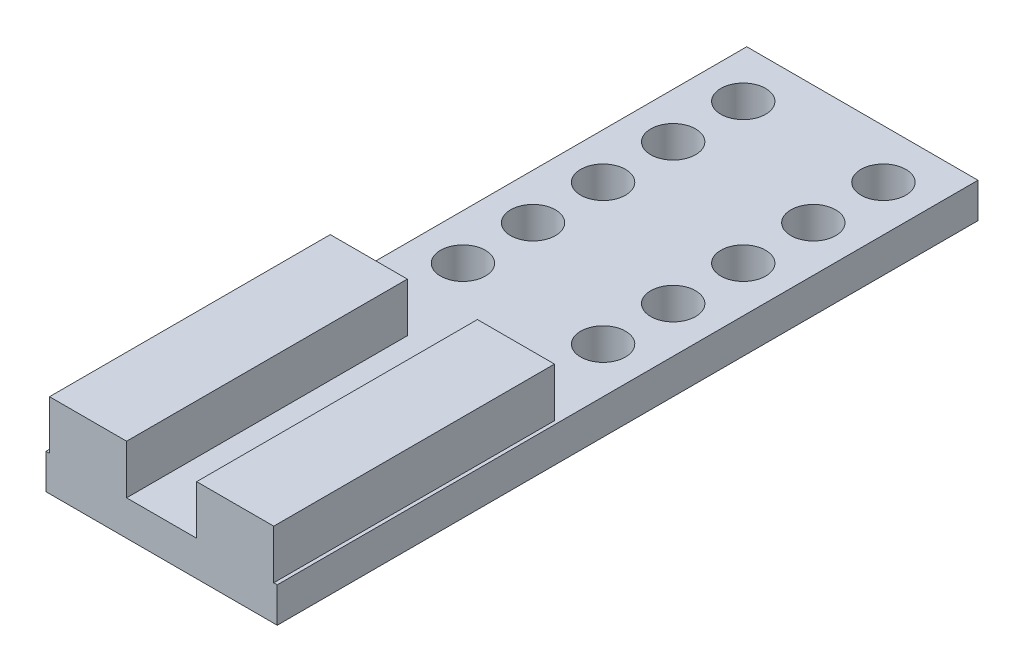
SolidWorks part; units mm, degrees
ref_plane "Front Plane" through (0, 0, 0) normal (0, 0, 1) x (1, 0, 0)
ref_plane "Top Plane" through (0, 0, 0) normal (0, 1, 0) x (1, 0, 0)
ref_plane "Right Plane" through (0, 0, 0) normal (1, 0, 0) x (0, 0, -1)
sketch "Sketch1" plane through (0, 0, 0) normal (0, 1, 0) x (1, 0, 0)
  line L1 (-8.25, 25) -> (8.25, 25)
  line L2 (-8.25, 25) -> (-8.25, -25)
  line L3 (-8.25, -25) -> (8.25, -25)
  line L4 (8.25, 25) -> (8.25, -25)
  point P4 (0, 25)
  point P6 (-8.25, 0)
  dimension "D1" = 16.5
  dimension "D2" = 50
extrude "Boss-Extrude1" add sketch "Sketch1" against normal blind 2.5
sketch "Sketch2" plane through (0, 0, 0) normal (0, 1, 0) x (1, 0, 0)
  line L0 (-8, -4.9674) -> (-2.5, -4.9674)
  line L1 (-2.5, -4.9674) -> (-2.5, -25)
  line L2 (-2.5, -25) -> (-8, -25)
  line L3 (-8, -25) -> (-8, -4.9674)
  line L4 (2.5, -4.9674) -> (8, -4.9674)
  line L5 (8, -4.9674) -> (8, -25)
  line L6 (8, -25) -> (2.5, -25)
  line L7 (2.5, -25) -> (2.5, -4.9674)
  line L8 (-8, -4.9674) -> (8, -4.9674) construction
  line L9 (-8.25, -25) -> (8.25, -25) construction
  point P8 (5.25, -25)
  point P9 (-5.25, -25)
  point P10 (0, -4.9674)
  dimension "D1" = 5.5
  dimension "D2" = 10.5
  dimension "D3" = 0
extrude "Boss-Extrude2" add sketch "Sketch2" along normal blind 3.5
sketch "Sketch4" plane through (0, 0, 0) normal (0, 1, 0) x (1, 0, 0)
  line L0 (8.25, 25) -> (-8.25, 25) construction
  line L1 (0, 0) -> (0, 26.8805) construction
  circle A0 centre (-5, 21.5) radius 1.6
  circle A2 centre (5, 21.5) radius 1.6
  dimension "D1" = 3.2
  dimension "D2" = 3.5
  dimension "D3" = 5
extrude "Cut-Extrude1" cut sketch "Sketch4" against normal through all
pattern_linear "LPattern1" count 5 spacing 5 along (0, 0, 1) of "Cut-Extrude1"
